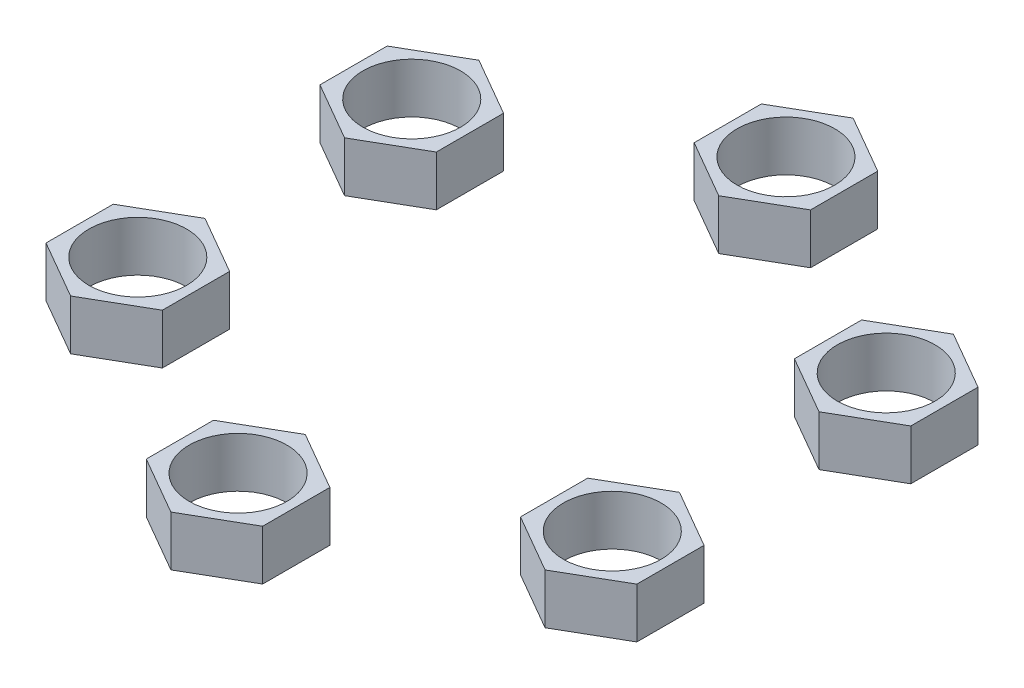
SolidWorks part; units mm, degrees
ref_plane "Front Plane" through (0, 0, 0) normal (0, 0, 1) x (1, 0, 0)
ref_plane "Top Plane" through (0, 0, 0) normal (0, 1, 0) x (1, 0, 0)
ref_plane "Right Plane" through (0, 0, 0) normal (1, 0, 0) x (0, 0, -1)
sketch "Sketch1" plane through (0, 0, 0) normal (0, 1, 0) x (1, 0, 0)
  line L0 (14.294, 8.2527) -> (18.9399, 5.5703)
  line L1 (0, 16.5053) -> (4.6459, 19.1876)
  line L2 (4.6459, 19.1876) -> (4.6459, 24.5523)
  line L3 (4.6459, 24.5523) -> (0, 27.2346)
  line L4 (0, 27.2346) -> (-4.6459, 24.5523)
  line L5 (-4.6459, 24.5523) -> (-4.6459, 19.1876)
  line L6 (-4.6459, 19.1876) -> (0, 16.5053)
  line L7 (18.9399, 5.5703) -> (23.5859, 8.2527)
  line L8 (23.5859, 8.2527) -> (23.5859, 13.6173)
  line L9 (23.5859, 13.6173) -> (18.9399, 16.2996)
  line L10 (18.9399, 16.2996) -> (14.294, 13.6173)
  line L11 (14.294, 13.6173) -> (14.294, 8.2527)
  line L12 (14.294, -8.2527) -> (14.294, -13.6173)
  line L13 (14.294, -13.6173) -> (18.9399, -16.2996)
  line L14 (18.9399, -16.2996) -> (23.5859, -13.6173)
  line L15 (23.5859, -13.6173) -> (23.5859, -8.2527)
  line L16 (23.5859, -8.2527) -> (18.9399, -5.5703)
  line L17 (18.9399, -5.5703) -> (14.294, -8.2527)
  line L18 (0, -16.5053) -> (-4.6459, -19.1876)
  line L19 (-4.6459, -19.1876) -> (-4.6459, -24.5523)
  line L20 (-4.6459, -24.5523) -> (0, -27.2346)
  line L21 (0, -27.2346) -> (4.6459, -24.5523)
  line L22 (4.6459, -24.5523) -> (4.6459, -19.1876)
  line L23 (4.6459, -19.1876) -> (0, -16.5053)
  line L24 (-14.294, -8.2527) -> (-18.9399, -5.5703)
  line L25 (-18.9399, -5.5703) -> (-23.5859, -8.2527)
  line L26 (-23.5859, -8.2527) -> (-23.5859, -13.6173)
  line L27 (-23.5859, -13.6173) -> (-18.9399, -16.2996)
  line L28 (-18.9399, -16.2996) -> (-14.294, -13.6173)
  line L29 (-14.294, -13.6173) -> (-14.294, -8.2527)
  line L30 (-14.294, 8.2527) -> (-14.294, 13.6173)
  line L31 (-14.294, 13.6173) -> (-18.9399, 16.2996)
  line L32 (-18.9399, 16.2996) -> (-23.5859, 13.6173)
  line L33 (-23.5859, 13.6173) -> (-23.5859, 8.2527)
  line L34 (-23.5859, 8.2527) -> (-18.9399, 5.5703)
  line L35 (-18.9399, 5.5703) -> (-14.294, 8.2527)
  circle A0 centre (18.9399, 10.935) radius 4.6459 construction
  circle A1 centre (0, 0) radius 16 construction
  circle A2 centre (0, -21.87) radius 3.9
  circle A3 centre (-18.9399, -10.935) radius 3.9
  circle A4 centre (-18.9399, 10.935) radius 3.9
  circle A5 centre (0, 21.87) radius 3.9
  circle A6 centre (18.9399, 10.935) radius 3.9
  circle A7 centre (18.9399, -10.935) radius 3.9
  circle A8 centre (0, 21.87) radius 4.6459 construction
  circle A9 centre (18.9399, -10.935) radius 4.6459 construction
  circle A10 centre (0, -21.87) radius 4.6459 construction
  circle A11 centre (-18.9399, -10.935) radius 4.6459 construction
  circle A12 centre (-18.9399, 10.935) radius 4.6459 construction
  point P16 (0, 0)
  point P65 (0, 0)
  dimension "D1" = 6
extrude "Boss-Extrude2" add sketch "Sketch1" along normal blind 4
